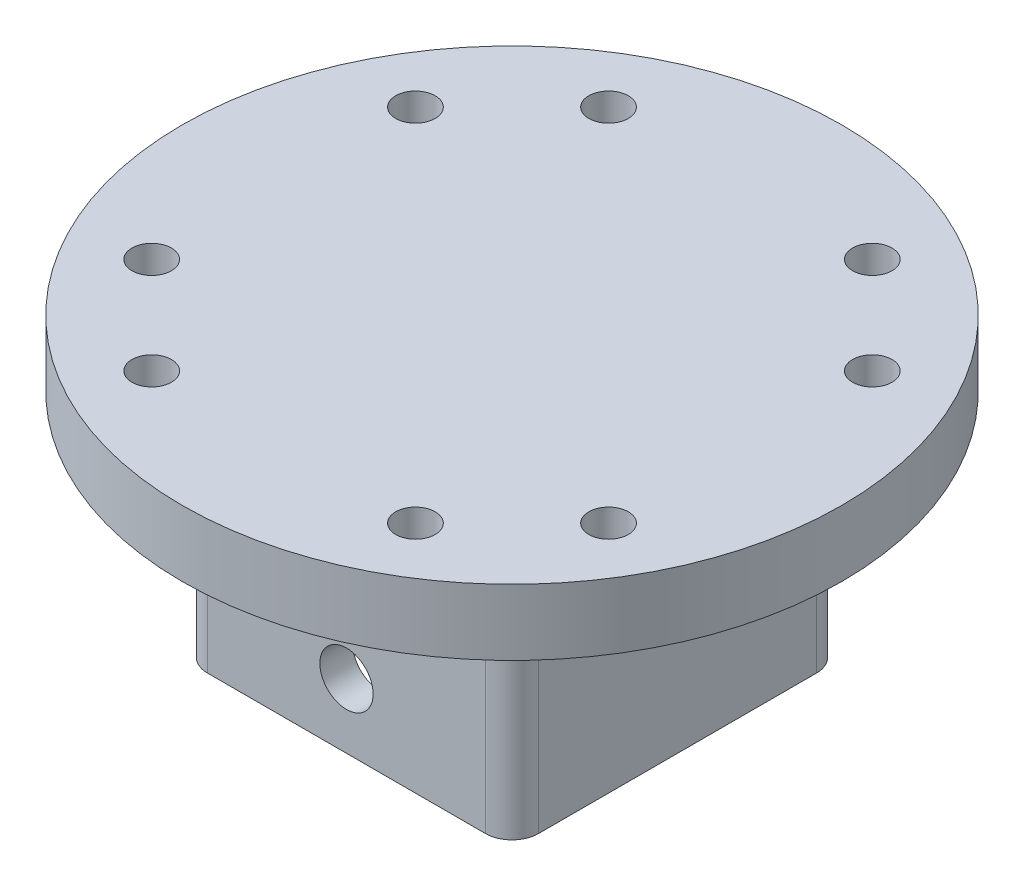
SolidWorks part; units mm, degrees
ref_plane "Front Plane" through (0, 0, 0) normal (0, 0, 1) x (1, 0, 0)
ref_plane "Top Plane" through (0, 0, 0) normal (0, 1, 0) x (1, 0, 0)
ref_plane "Right Plane" through (0, 0, 0) normal (1, 0, 0) x (0, 0, -1)
sketch "Sketch1" plane through (0, 0, 0) normal (0, 1, 0) x (1, 0, 0)
  circle A0 centre (0, 0) radius 31.75 construction
  circle A1 centre (0, 0) radius 15.9385 construction
  circle A2 centre (0, 0) radius 12.7635 construction
  dimension "D1" = 63.5
  dimension "D2" = 25.527
  dimension "D3" = 3.175
sketch "Sketch6" plane through (0, 0, 0) normal (0, 0, 1) x (1, 0, 0)
  line L0 (0, -18.7832) -> (0, 8.1093) construction
sketch "Sketch2" plane through (0, 0, 0) normal (0, 1, 0) x (1, 0, 0)
  circle A0 centre (0, 0) radius 31.75 construction
  circle A1 centre (0, 0) radius 31.75
extrude "Boss-Extrude1" add sketch "Sketch2" along normal blind 6.35
sketch "Sketch3" plane through (0, 0, 0) normal (0, 1, 0) x (1, 0, 0)
  line L0 (15.9385, 15.9385) -> (15.9385, -15.9385)
  line L1 (15.9385, -15.9385) -> (-15.9385, -15.9385)
  line L2 (-15.9385, -15.9385) -> (-15.9385, 15.9385)
  line L3 (-15.9385, 15.9385) -> (15.9385, 15.9385)
  circle A2 centre (0, 0) radius 15.9385 construction
extrude "Boss-Extrude2" add sketch "Sketch3" against normal blind 22.225
sketch "Sketch4" plane through (0, 0, 0) normal (0, 1, 0) x (1, 0, 0)
  line L0 (12.7635, 12.7635) -> (12.7635, -12.7635)
  line L1 (12.7635, -12.7635) -> (-12.7635, -12.7635)
  line L2 (-12.7635, -12.7635) -> (-12.7635, 12.7635)
  line L3 (-12.7635, 12.7635) -> (12.7635, 12.7635)
  circle A2 centre (0, 0) radius 12.7635 construction
extrude "Cut-Extrude1" cut sketch "Sketch4" against normal through all
sketch "Sketch5" plane through (0, 0, 0) normal (0, 1, 0) x (1, 0, 0)
  line L0 (0, 0) -> (37.5473, 0) construction
  line L1 (0, 0) -> (21.997, 12.7) construction
  circle A1 centre (21.997, 12.7) radius 1.9
  circle A2 centre (21.997, -12.7) radius 1.9
  dimension "D5" = 3.8
  dimension "D2" = 30
  dimension "D3" = 25.4
extrude "Cut-Extrude2" cut sketch "Sketch5" along normal through all
sketch "Sketch7" plane through (0, 0, 0) normal (0, 0, 1) x (1, 0, 0)
  line L0 (0, -18.7832) -> (0, 8.1093) construction
  circle A0 centre (0, -16.002) radius 2.5635
  dimension "D1" = 5.127
  dimension "D2" = 16.002
extrude "Cut-Extrude3" cut sketch "Sketch7" against normal through all both and the other way through all
pattern_circular "CirPattern2" count 4 over 360 about axis through (0, 0, 0) along (0, 1, 0) of "Cut-Extrude2"
fillet "Fillet2" radius 2.54 4 edges at (-15.9385, -11.1125, 15.9385) (15.9385, -11.1125, 15.9385) (15.9385, -11.1125, -15.9385) (-15.9385, -11.1125, -15.9385)
fillet "Fillet3" radius 2.54 8 edges at (15.1946, 0, -15.1946) (15.9385, 0, 0) (15.1946, 0, 15.1946) (0, 0, 15.9385) (-15.1946, 0, 15.1946) (-15.9385, 0, 0) (-15.1946, 0, -15.1946) (0, 0, -15.9385)
equation "\"tightTol\"= 0.005in"
equation "\"normTol\"= 0.01in"
equation "\"looseTol\"= 0.02in"
equation "\"D2@Sketch1\"=\"tightTol\"+1.000000in"
equation "\"D5@Sketch5\"=3.8mm"
equation "\"D1@Sketch7\"=\"tightTol\"+5mm"
equation "\"D2@Sketch7\"=\"tightTol\"+0.625000in"
